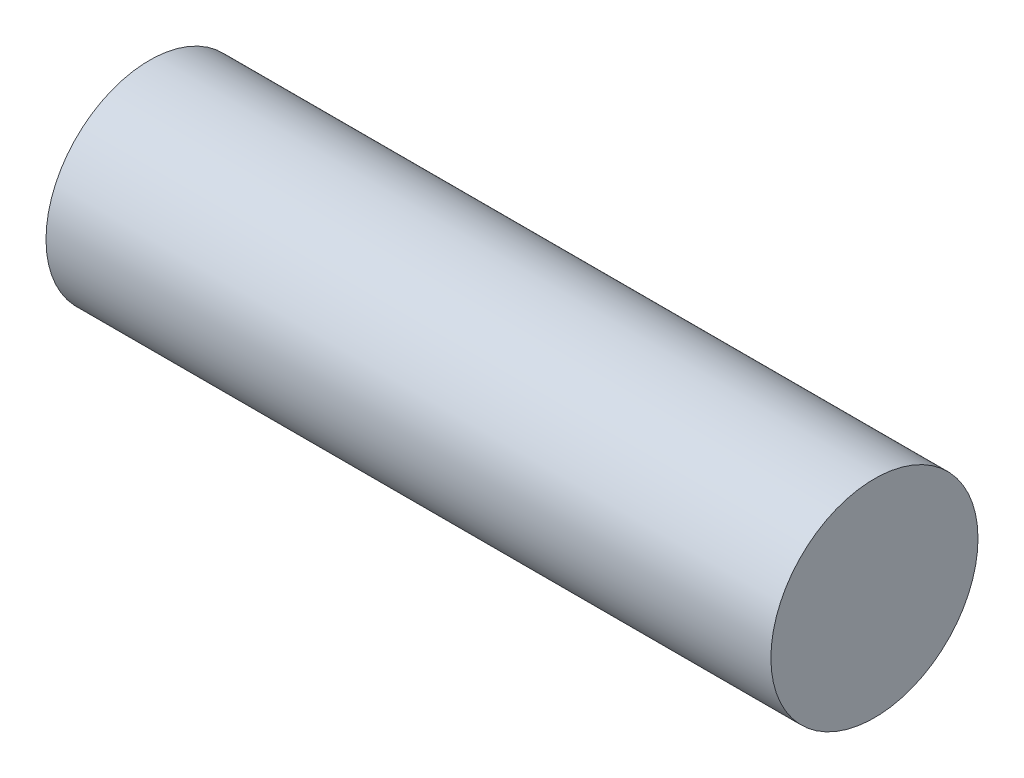
SolidWorks part; units mm, degrees
ref_plane "Front Plane" through (0, 0, 0) normal (0, 0, 1) x (1, 0, 0)
ref_plane "Top Plane" through (0, 0, 0) normal (0, 1, 0) x (1, 0, 0)
ref_plane "Right Plane" through (0, 0, 0) normal (1, 0, 0) x (0, 0, -1)
sketch "Sketch1" plane through (0, 0, 0) normal (1, 0, 0) x (0, 0, -1)
  circle A0 centre (0, 0) radius 12.7
  dimension "D1" = 25.4
extrude "Extrude1" add sketch "Sketch1" along normal mid plane 88.9
